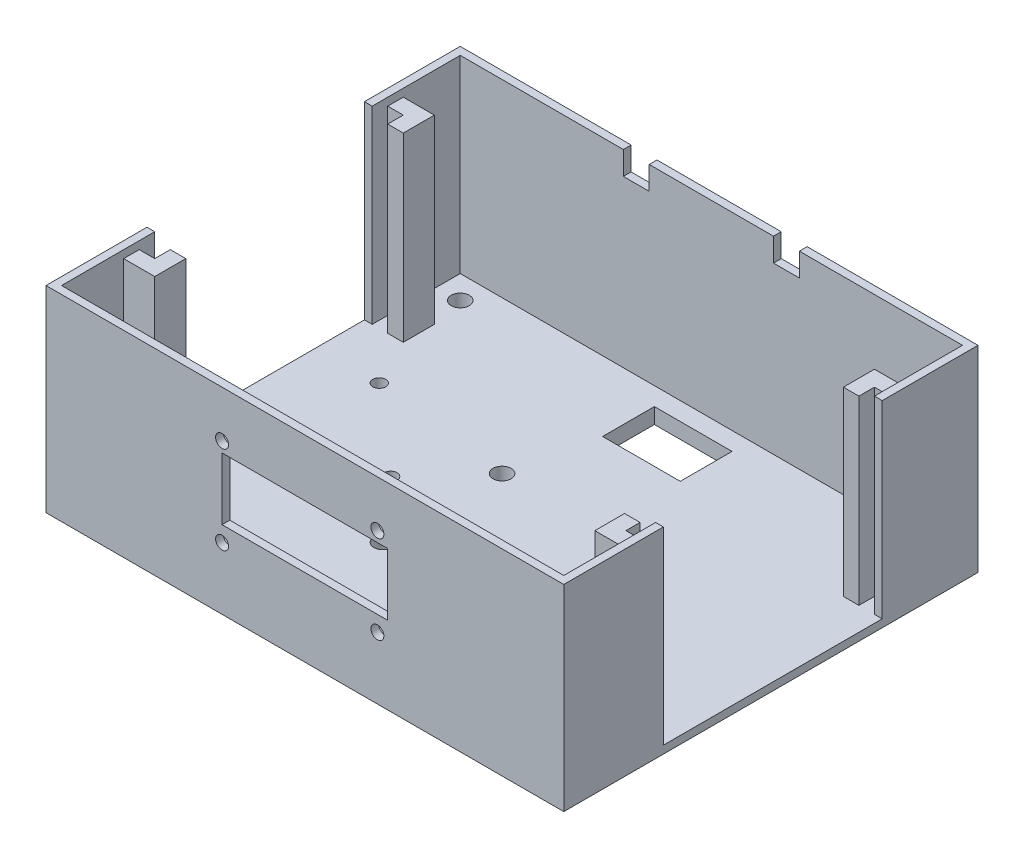
SolidWorks part; units mm, degrees
ref_plane "Plan de face" through (0, 0, 0) normal (0, 0, 1) x (1, 0, 0)
ref_plane "Plan de dessus" through (0, 0, 0) normal (0, 1, 0) x (1, 0, 0)
ref_plane "Plan de droite" through (0, 0, 0) normal (1, 0, 0) x (0, 0, -1)
sketch "Esquisse1" plane through (0, 0, 0) normal (0, 1, 0) x (1, 0, 0)
  line L1 (0, 0) -> (100, 0)
  line L2 (0, 0) -> (0, 80)
  line L3 (0, 80) -> (100, 80)
  line L4 (100, 0) -> (100, 80)
  line L5 (42.5, 75) -> (57.5, 75)
  line L6 (42.5, 75) -> (42.5, 65)
  line L7 (42.5, 65) -> (57.5, 65)
  line L8 (57.5, 75) -> (57.5, 65)
  circle A0 centre (6, 74) radius 1.75
  circle A1 centre (94, 74) radius 1.75
  circle A2 centre (94, 6) radius 1.75
  circle A3 centre (6, 6) radius 1.75
  circle A4 centre (88, 26.0817) radius 1.75
  circle A5 centre (39, 26.0817) radius 1.75
  circle A6 centre (39, 49.0817) radius 1.75
  circle A7 centre (28.72, 37.85) radius 1.25
  circle A8 centre (12, 52.36) radius 1.25
  dimension "D7" = 3.5
  dimension "D8" = 3.5
  dimension "D9" = 3.5
  dimension "D10" = 3.5
  dimension "D11" = 6
  dimension "D12" = 6
  dimension "D13" = 6
  dimension "D14" = 6
  dimension "D15" = 6
  dimension "D16" = 6
  dimension "D17" = 6
  dimension "D18" = 6
  dimension "D19" = 3.5
  dimension "D20" = 3.5
  dimension "D21" = 3.5
  dimension "D22" = 23
  dimension "D23" = 49
  dimension "D24" = 12
  dimension "D25" = 2.5
  dimension "D26" = 2.5
  dimension "D1" = 100
  dimension "D2" = 80
  dimension "D3" = 10
  dimension "D4" = 15
  dimension "D5" = 42.5
  dimension "D6" = 5
extrude "Boss.-Extru.1" add sketch "Esquisse1" along normal blind 1.5
sketch "Esquisse2" plane through (0, 1.5, 0) normal (0, 1, 0) x (1, 0, 0)
  line L0 (0, 0) -> (100, 0) construction
  line L1 (1.5, 78.5) -> (98.5, 78.5)
  line L2 (1.5, 78.5) -> (1.5, 67.5)
  line L3 (1.5, 1.5) -> (98.5, 1.5)
  line L4 (98.5, 78.5) -> (98.5, 67.5)
  line L5 (0, 80) -> (100, 80)
  line L6 (0, 80) -> (0, 61.5)
  line L7 (0, 0) -> (100, 0)
  line L8 (100, 80) -> (100, 61.5)
  line L9 (100, 0) -> (100, 80) construction
  line L10 (1.5, 61.5) -> (0, 61.5)
  line L11 (1.5, 13.5) -> (7.5, 13.5)
  line L12 (1.5, 13.5) -> (1.5, 1.5)
  line L13 (1.5, 16.5) -> (4.5, 16.5)
  line L14 (7.5, 13.5) -> (7.5, 16.5)
  line L15 (1.5, 64.5) -> (1.5, 61.5)
  line L16 (7.5, 16.5) -> (7.5, 19.5)
  line L17 (7.5, 19.5) -> (4.5, 19.5)
  line L18 (4.5, 16.5) -> (4.5, 19.5)
  line L19 (1.5, 67.5) -> (7.5, 67.5)
  line L20 (95.5, 16.5) -> (98.5, 16.5)
  line L21 (1.5, 64.5) -> (4.5, 64.5)
  line L22 (7.5, 67.5) -> (7.5, 64.5)
  line L23 (98.5, 67.5) -> (92.5, 67.5)
  line L24 (7.5, 64.5) -> (7.5, 61.5)
  line L25 (7.5, 61.5) -> (4.5, 61.5)
  line L26 (4.5, 64.5) -> (4.5, 61.5)
  line L27 (1.5, 19.5) -> (0, 19.5)
  line L28 (1.5, 19.5) -> (1.5, 16.5)
  line L29 (0, 19.5) -> (0, 0)
  line L30 (98.5, 13.5) -> (98.5, 1.5)
  line L31 (98.5, 64.5) -> (95.5, 64.5)
  line L32 (92.5, 67.5) -> (92.5, 64.5)
  line L33 (98.5, 16.5) -> (98.5, 19.2371)
  line L34 (92.5, 64.5) -> (92.5, 61.5)
  line L35 (92.5, 61.5) -> (95.5, 61.5)
  line L36 (95.5, 64.5) -> (95.5, 61.5)
  line L37 (98.5, 13.5) -> (92.5, 13.5)
  line L38 (98.5, 19.2371) -> (100, 19.2371)
  line L40 (92.5, 13.5) -> (92.5, 16.5)
  line L42 (92.5, 16.5) -> (92.5, 19.2371)
  line L43 (92.5, 19.2371) -> (95.5, 19.2371)
  line L44 (95.5, 16.5) -> (95.5, 19.2371)
  line L46 (98.5, 61.5) -> (100, 61.5)
  line L48 (100, 19.2371) -> (100, 0)
  line L49 (98.5, 64.5) -> (98.5, 61.5)
  dimension "D1" = 1.5
  dimension "D2" = 1.5
  dimension "D3" = 1.5
  dimension "D4" = 1.5
  dimension "D5" = 12
  dimension "D6" = 3
  dimension "D7" = 3
  dimension "D8" = 6
  dimension "D9" = 3
  dimension "D10" = 6
  dimension "D11" = 3
  dimension "D12" = 3
  dimension "D13" = 3
  dimension "D14" = 48
  dimension "D15" = 6
  dimension "D16" = 3
  dimension "D17" = 3
  dimension "D18" = 3
  dimension "D19" = 6
  dimension "D20" = 3
  dimension "D21" = 2.7371
  dimension "D22" = 3
  dimension "D23" = 12
  dimension "D24" = 3
  dimension "D25" = 48
extrude "Boss.-Extru.2" add sketch "Esquisse2" along normal blind 36.5
sketch "Esquisse3" plane through (0, 0, 0) normal (0, 0, 1) x (1, 0, 0)
  line L0 (100, 38) -> (100, 0) construction
  line L1 (34, 27) -> (66, 27)
  line L2 (34, 27) -> (34, 15)
  line L3 (34, 15) -> (66, 15)
  line L4 (66, 27) -> (66, 15)
  line L6 (0, 0) -> (100, 0) construction
  circle A0 centre (34, 29) radius 1.25
  circle A1 centre (34, 12) radius 1.25
  circle A2 centre (64, 12) radius 1.25
  circle A3 centre (64, 29) radius 1.25
  dimension "D5" = 2.5
  dimension "D6" = 2.5
  dimension "D7" = 2.5
  dimension "D8" = 2.5
  dimension "D9" = 2
  dimension "D10" = 2
  dimension "D11" = 3
  dimension "D12" = 3
  dimension "D1" = 12
  dimension "D2" = 32
  dimension "D3" = 34
  dimension "D4" = 15
  dimension "D13" = 2
  dimension "D14" = 2
extrude "Enlèv. mat.-Extru.1" cut sketch "Esquisse3" against normal blind 5
sketch "Esquisse4" plane through (0, 0, 0) normal (0, -1, 0) x (1, 0, 0)
  line L0 (100, -80) -> (0, -80) construction
  line L1 (2, -2) -> (98, -2)
  line L2 (2, -2) -> (2, -78)
  line L3 (2, -78) -> (98, -78)
  line L4 (98, -2) -> (98, -78)
  line L5 (42.5, -65) -> (57.5, -65)
  line L6 (42.5, -65) -> (42.5, -75)
  line L7 (42.5, -75) -> (57.5, -75)
  line L8 (57.5, -65) -> (57.5, -75)
  line L9 (0, -80) -> (0, 0) construction
  line L10 (0, 0) -> (100, 0) construction
  line L11 (100, 0) -> (100, -80) construction
  circle A0 centre (6, -6) radius 1.75
  circle A1 centre (6, -74) radius 1.75
  circle A2 centre (94, -74) radius 1.75
  circle A3 centre (94, -6) radius 1.75
  circle A4 centre (88, -26.0817) radius 1.75
  circle A5 centre (39, -49.0817) radius 1.75
  circle A6 centre (39, -26.0817) radius 1.75
  circle A7 centre (28.72, -37.85) radius 1.25
  circle A8 centre (12, -52.36) radius 1.25
  dimension "D5" = 3.5
  dimension "D6" = 3.5
  dimension "D9" = 2.5
  dimension "D1" = 2
  dimension "D2" = 2
  dimension "D3" = 2
  dimension "D4" = 2
  dimension "D7" = 23
  dimension "D8" = 49
extrude "Boss.-Extru.3" add sketch "Esquisse4" along normal blind 1.5
sketch "Esquisse5" plane through (0, 38, 0) normal (0, 1, 0) x (1, 0, 0)
  line L0 (7.5, 61.5) -> (7.5, 67.5) construction
  line L1 (1.5, 67.5) -> (7.5, 67.5)
  line L2 (1.5, 67.5) -> (1.5, 64.5)
  line L3 (1.5, 64.5) -> (4.5, 64.5)
  line L4 (7.5, 67.5) -> (7.5, 64.5)
  line L5 (4.5, 19.5) -> (4.5, 16.5) construction
  line L6 (7.5, 61.5) -> (4.5, 61.5)
  line L7 (7.5, 61.5) -> (7.5, 64.5)
  line L8 (1.5, 16.5) -> (4.5, 16.5)
  line L9 (4.5, 61.5) -> (4.5, 64.5)
  line L10 (1.5, 16.5) -> (1.5, 13.5)
  line L11 (1.5, 13.5) -> (7.5, 13.5)
  line L12 (7.5, 16.5031) -> (7.5, 13.5)
  line L13 (92.5, 13.5) -> (98.5, 13.5) construction
  line L14 (7.5, 16.5031) -> (7.5, 19.5)
  line L15 (7.5, 19.5) -> (4.5, 19.5)
  line L16 (4.5, 16.5) -> (4.5, 19.5)
  line L17 (7.5, 19.5) -> (4.5, 19.5) construction
  line L18 (92.5, 19.2371) -> (95.5, 19.2371)
  line L20 (98.5, 67.5) -> (92.5, 67.5) construction
  line L21 (95.5, 19.2371) -> (95.5, 16.5)
  line L22 (98.5, 16.5) -> (95.5, 16.5)
  line L23 (98.5, 16.5) -> (98.5, 13.5)
  line L24 (98.5, 13.5) -> (92.5, 13.5)
  line L25 (92.5, 19.2371) -> (92.5, 13.5)
  line L26 (92.5, 19.2371) -> (92.5, 13.5) construction
  line L27 (95.5, 61.5) -> (92.5, 61.5)
  line L28 (95.5, 61.5) -> (95.5, 64.5)
  line L29 (95.5, 67.5) -> (92.5, 67.5)
  line L30 (92.5, 61.5) -> (92.5, 67.5)
  line L32 (95.5, 67.5) -> (98.5, 67.5)
  line L34 (95.5, 64.5) -> (98.5, 64.5)
  line L35 (98.5, 67.5) -> (98.5, 64.5)
extrude "Enlèv. mat.-Extru.2" cut sketch "Esquisse5" against normal blind 1.5
sketch "Esquisse6" plane through (0, 0, -78.5) normal (0, 0, 1) x (1, 0, 0)
  line L0 (1.5, 38) -> (98.5, 38) construction
  line L1 (33, 38) -> (38, 38)
  line L2 (33, 38) -> (33, 33.5)
  line L3 (33, 33.5) -> (38, 33.5)
  line L4 (38, 38) -> (38, 33.5)
  line L5 (1.5, 38) -> (1.5, 1.5) construction
  line L6 (62, 38) -> (67, 38)
  line L7 (62, 38) -> (62, 33.5)
  line L8 (62, 33.5) -> (67, 33.5)
  line L9 (67, 38) -> (67, 33.5)
  dimension "D1" = 4.5
  dimension "D2" = 5
  dimension "D3" = 24
  dimension "D4" = 5
  dimension "D5" = 4.5
  dimension "D6" = 31.5
extrude "Enlèv. mat.-Extru.3" cut sketch "Esquisse6" against normal blind 10
equation "\"38.5.00mm\"=40"
